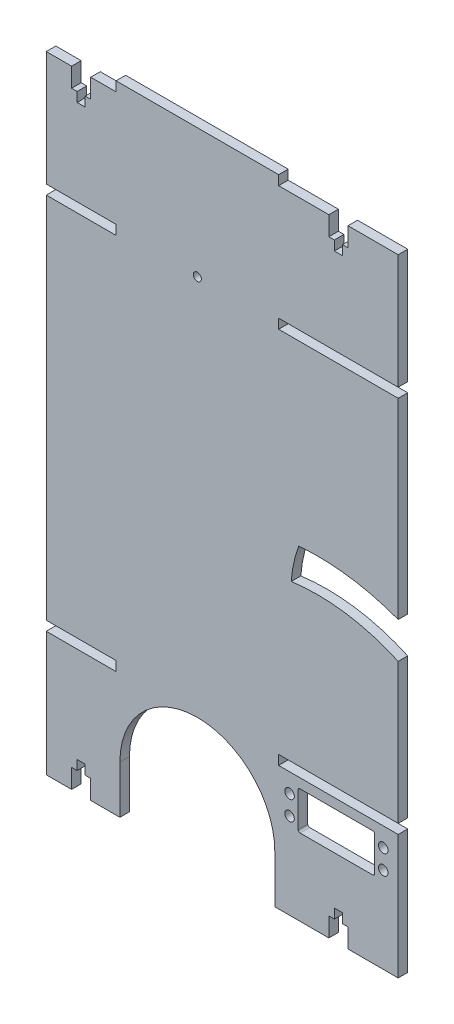
SolidWorks part; units mm, degrees
ref_plane "Front Plane" through (0, 0, 0) normal (0, 0, 1) x (1, 0, 0)
ref_plane "Top Plane" through (0, 0, 0) normal (0, 1, 0) x (1, 0, 0)
ref_plane "Right Plane" through (0, 0, 0) normal (1, 0, 0) x (0, 0, -1)
sketch "Sketch2" plane through (0, 0, 0) normal (0, 0, 1) x (1, 0, 0)
  line L1 (-92, 166.25) -> (92, 166.25)
  line L2 (-92, 166.25) -> (-92, -166.25)
  line L3 (-92, -166.25) -> (92, -166.25)
  line L4 (92, 166.25) -> (92, -166.25)
  line L5 (-92, 166.25) -> (92, -166.25) construction
  line L6 (-92, -166.25) -> (92, 166.25) construction
  point P0 (0, 0)
  dimension "D1" = 332.5
  dimension "D2" = 184
extrude "Boss-Extrude1" add sketch "Sketch2" along normal blind 5
sketch "Sketch3" plane through (0, 0, 5) normal (0, 0, 1) x (1, 0, 0)
  line L0 (-92, 166.25) -> (-92, -166.25) construction
  line L1 (-55.5, -101.25) -> (-92, -101.25)
  line L2 (-55.5, -101.25) -> (-55.5, -96.25)
  line L3 (-55.5, -96.25) -> (-92, -96.25)
  line L4 (-92, -101.25) -> (-92, -96.25)
  line L5 (-55.5, -101.25) -> (-92, -96.25) construction
  line L6 (-55.5, -96.25) -> (-92, -101.25) construction
  line L7 (-98, -96.25) -> (-55.5, -96.25) construction
  line L8 (92, -166.25) -> (92, 166.25) construction
  line L9 (29.5, -96.25) -> (92, -96.25)
  line L10 (29.5, -96.25) -> (29.5, -101.25)
  line L11 (29.5, -101.25) -> (92, -101.25)
  line L12 (92, -96.25) -> (92, -101.25)
  line L13 (29.5, -96.25) -> (92, -101.25) construction
  line L14 (29.5, -101.25) -> (92, -96.25) construction
  line L15 (29.5, -101.25) -> (92, -101.25) construction
  line L17 (29.5, 96.25) -> (92, 96.25) construction
  line L21 (-55.5, 161.25) -> (-92, 161.25)
  line L22 (-55.5, 161.25) -> (-55.5, 166.25)
  line L23 (-55.5, 166.25) -> (-92, 166.25)
  line L24 (-92, 161.25) -> (-92, 166.25)
  line L25 (-55.5, 161.25) -> (-92, 166.25) construction
  line L26 (-55.5, 166.25) -> (-92, 161.25) construction
  line L27 (29.5, 161.25) -> (92, 161.25)
  line L28 (29.5, 161.25) -> (29.5, 166.25)
  line L29 (29.5, 166.25) -> (92, 166.25)
  line L30 (92, 161.25) -> (92, 166.25)
  line L31 (29.5, 161.25) -> (92, 166.25) construction
  line L32 (29.5, 166.25) -> (92, 161.25) construction
  line L33 (29.5, 101.25) -> (92, 101.25)
  line L34 (27.5, -141.25) -> (27.5, -166.25)
  line L37 (-92, -166.25) -> (92, -166.25) construction
  line L38 (27.5, -166.25) -> (-53.5, -166.25)
  line L39 (-53.5, -166.25) -> (-53.5, -141.25)
  line L40 (29.5, 101.25) -> (29.5, 96.25)
  line L41 (29.5, 96.25) -> (92, 96.25)
  line L42 (92, 101.25) -> (92, 96.25)
  line L43 (29.5, 101.25) -> (92, 96.25) construction
  line L44 (29.5, 96.25) -> (92, 101.25) construction
  line L45 (-98, 101.25) -> (-55.5, 101.25) construction
  line L46 (-55.5, 96.25) -> (-92, 96.25)
  line L47 (-55.5, 96.25) -> (-55.5, 101.25)
  line L48 (-55.5, 101.25) -> (-92, 101.25)
  line L49 (-92, 96.25) -> (-92, 101.25)
  line L50 (-55.5, 96.25) -> (-92, 101.25) construction
  line L51 (-55.5, 101.25) -> (-92, 96.25) construction
  arc A2 (27.5, -141.25) -> (-53.5, -141.25) centre (-13, -141.25) ccw
  point P7 (-73.75, -98.75)
  point P17 (60.75, -98.75)
  point P32 (-73.75, 163.75)
  point P39 (60.75, 163.75)
  point P45 (60.75, 98.75)
  point P54 (-73.75, 98.75)
extrude "Cut-Extrude1" cut sketch "Sketch3" against normal blind 5
sketch "Sketch4" plane through (0, 0, 5) normal (0, 0, 1) x (1, 0, 0)
  line L0 (-73.75, 161.25) -> (-73.75, 123.1738) construction
  line L1 (-92, 161.25) -> (-55.5, 161.25) construction
  line L2 (69.7422, 161.25) -> (69.7422, -166.25) construction
  line L3 (-92, 0) -> (92, 0) construction
  line L5 (-13, 166.25) -> (-13, 111.1543) construction
  line L6 (29.5, 166.25) -> (-55.5, 166.25) construction
  line L7 (29.5, 161.25) -> (92, 161.25) construction
  line L8 (27.5, -166.25) -> (92, -166.25) construction
  line L9 (69.7422, -2.5) -> (44.3363, -2.5) construction
  line L10 (92, -96.25) -> (92, 96.25) construction
  line L11 (0, 0) -> (0, 111.1543) construction
  line L12 (0, 111.1543) -> (-13, 111.1543) construction
  line L13 (-6.5, 111.1543) -> (-6.5, 119.3244) construction
  line L14 (60.75, 161.25) -> (60.75, 140.689) construction
  line L15 (55.75, 161.25) -> (55.75, 151.25)
  line L16 (55.75, 151.25) -> (58.65, 151.25)
  line L17 (58.65, 151.25) -> (58.65, 146.25)
  line L18 (58.65, 146.25) -> (62.85, 146.25)
  line L19 (55.75, 161.25) -> (65.75, 161.25)
  line L20 (62.85, 151.25) -> (62.85, 146.25)
  line L21 (65.75, 151.25) -> (62.85, 151.25)
  line L22 (65.75, 161.25) -> (65.75, 151.25)
  line L23 (-78.75, 161.25) -> (-78.75, 151.25)
  line L24 (-78.75, 151.25) -> (-75.85, 151.25)
  line L25 (-75.85, 151.25) -> (-75.85, 146.25)
  line L26 (-68.75, 161.25) -> (-78.75, 161.25)
  line L27 (-71.65, 146.25) -> (-75.85, 146.25)
  line L28 (-71.65, 151.25) -> (-71.65, 146.25)
  line L29 (-68.75, 151.25) -> (-71.65, 151.25)
  line L30 (-68.75, 161.25) -> (-68.75, 151.25)
  line L31 (60.75, -166.25) -> (60.75, -145.689) construction
  line L32 (65.75, -166.25) -> (65.75, -156.25)
  line L33 (65.75, -156.25) -> (62.85, -156.25)
  line L34 (62.85, -156.25) -> (62.85, -151.25)
  line L35 (55.75, -166.25) -> (65.75, -166.25)
  line L36 (58.65, -151.25) -> (62.85, -151.25)
  line L37 (58.65, -156.25) -> (58.65, -151.25)
  line L38 (55.75, -156.25) -> (58.65, -156.25)
  line L39 (55.75, -166.25) -> (55.75, -156.25)
  line L40 (-68.75, -166.25) -> (-68.75, -156.25)
  line L41 (-68.75, -156.25) -> (-71.65, -156.25)
  line L42 (-71.65, -156.25) -> (-71.65, -151.25)
  line L43 (-71.65, -151.25) -> (-75.85, -151.25)
  line L44 (-68.75, -166.25) -> (-78.75, -166.25)
  line L45 (-75.85, -156.25) -> (-75.85, -151.25)
  line L46 (-78.75, -156.25) -> (-75.85, -156.25)
  line L47 (-78.75, -166.25) -> (-78.75, -156.25)
  point P36 (60.75, 146.25)
  point P46 (-73.75, 146.25)
  point P57 (60.75, -151.25)
  point P66 (-73.75, -151.25)
  dimension "D1" = 10
  dimension "D2" = 5
  dimension "D3" = 2.9
  dimension "D4" = 5
extrude "Cut-Extrude2" cut sketch "Sketch4" against normal blind 10
sketch "Sketch5" plane through (0, 0, 5) normal (0, 0, 1) x (1, 0, 0)
  line L0 (-55.5, 98.75) -> (29.5, 98.75) construction
  line L1 (-55.5, 96.25) -> (-55.5, 101.25) construction
  line L2 (29.5, 96.25) -> (29.5, 101.25) construction
  circle A0 centre (-13, 98.75) radius 2.1
  dimension "D1" = 4.2
extrude "Cut-Extrude3" cut sketch "Sketch5" against normal blind 10
sketch "Sketch6" plane through (0, 0, 0) normal (0, 0, -1) x (-1, 0, 0)
  line L0 (-78.2, -106.25) -> (-41.2, -106.25)
  line L1 (-41.2, -106.25) -> (-40.7, -106.25)
  line L2 (-39.7, -107.25) -> (-39.7, -125.25)
  line L3 (-40.7, -126.25) -> (-78.7, -126.25)
  line L4 (-79.7, -125.25) -> (-79.7, -107.25)
  line L5 (-78.7, -106.25) -> (-78.2, -106.25)
  circle A0 centre (-35.2, -111.17) radius 2.5
  circle A1 centre (-35.2, -121.33) radius 2.5
  circle A2 centre (-84.2, -111.17) radius 2.5
  circle A3 centre (-84.2, -121.33) radius 2.5
  arc A4 (-40.7, -106.25) -> (-39.7, -107.25) centre (-40.7, -107.25) cw
  arc A5 (-39.7, -125.25) -> (-40.7, -126.25) centre (-40.7, -125.25) cw
  arc A6 (-78.7, -126.25) -> (-79.7, -125.25) centre (-78.7, -125.25) cw
  arc A7 (-79.7, -107.25) -> (-78.7, -106.25) centre (-78.7, -107.25) cw
extrude "Cut-Extrude4" cut sketch "Sketch6" against normal blind 20
sketch "Sketch7" plane through (0, 0, 5) normal (0, 0, 1) x (1, 0, 0)
  line L4 (92.0183, -3.9595) -> (92, -22.8853)
  line L5 (92, -96.25) -> (92, 96.25) construction
  arc A4 (92.0183, -3.9595) -> (39.9761, 3.3554) centre (49.7, -116.25) ccw
  arc A5 (92, -22.8853) -> (36.0805, -14.6589) centre (49.7, -116.25) ccw
  arc A6 (39.9761, 3.3554) -> (36.0805, -14.6589) centre (102.0215, -19.4902) ccw
extrude "Cut-Extrude6" cut sketch "Sketch7" against normal through all
